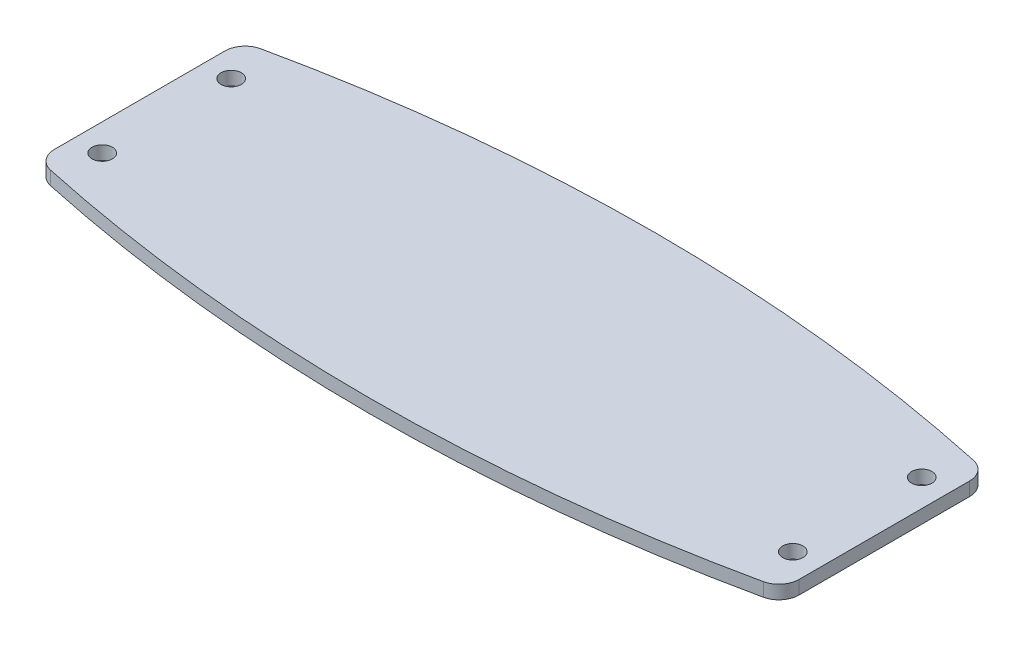
SolidWorks part; units mm, degrees
ref_plane "Спереди" through (0, 0, 0) normal (0, 0, 1) x (1, 0, 0)
ref_plane "Сверху" through (0, 0, 0) normal (0, 1, 0) x (1, 0, 0)
ref_plane "Справа" through (0, 0, 0) normal (1, 0, 0) x (0, 0, -1)
sketch "Эскиз1" plane through (0, 0, 0) normal (0, 1, 0) x (1, 0, 0)
  line L0 (-55, -2.4107) -> (-55, -27.5893)
  line L1 (0, 6.125) -> (0, -3.1451) construction
  line L2 (55, -2.4107) -> (55, -27.5893)
  line L3 (-55, -15) -> (55, -15) construction
  arc A0 (-52.6316, 0.5221) -> (52.6316, 0.5221) centre (0, -243.875) cw
  arc A1 (-52.6316, -30.5221) -> (52.6316, -30.5221) centre (0, 213.875) ccw
  circle A2 centre (-51, -5.4779) radius 1.5
  circle A3 centre (-51, -24.5221) radius 1.5
  circle A4 centre (51, -5.4779) radius 1.5
  circle A5 centre (51, -24.5221) radius 1.5
  arc A6 (55, -27.5893) -> (52.6316, -30.5221) centre (52, -27.5893) cw
  arc A7 (52.6316, 0.5221) -> (55, -2.4107) centre (52, -2.4107) cw
  arc A8 (-55, -27.5893) -> (-52.6316, -30.5221) centre (-52, -27.5893) ccw
  arc A9 (-52.6316, 0.5221) -> (-55, -2.4107) centre (-52, -2.4107) ccw
  point P4 (0, 0)
  point P22 (55, -30)
  point P25 (55, 0)
  point P28 (-55, -30)
  point P31 (-55, 0)
  dimension "D2" = 250
  dimension "D6" = 3
  dimension "D7" = 3
  dimension "D1" = 110
  dimension "D3" = 30
  dimension "D4" = 6
  dimension "D5" = 4
extrude "Бобышка-Вытянуть1" add sketch "Эскиз1" along normal blind 2
